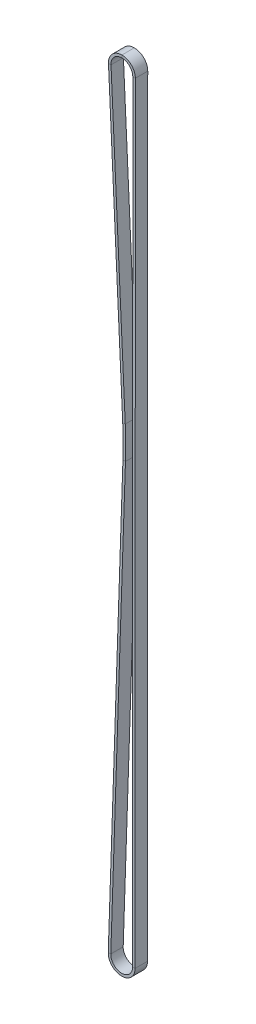
SolidWorks part; units mm, degrees
ref_plane "Front Plane" through (0, 0, 0) normal (0, 0, 1) x (1, 0, 0)
ref_plane "Top Plane" through (0, 0, 0) normal (0, 1, 0) x (1, 0, 0)
ref_plane "Right Plane" through (0, 0, 0) normal (1, 0, 0) x (0, 0, -1)
sketch "Sketch2" plane through (0, 0, 0) normal (0, 0, 1) x (1, 0, 0)
  line L0 (0, 0) -> (1, 0) construction
  line L1 (0, 0) -> (0, 1) construction
  line L3 (7.0911, -457.202) -> (7.2181, -0.002)
  line L4 (-7.2101, -0.338) -> (1.2395, -180.6057)
  line L5 (1.3637, -199.6863) -> (-7.3409, -456.9559)
  arc A0 (7.2181, -0.002) -> (-7.2101, -0.338) centre (0, 0) ccw
  arc A1 (-7.3409, -456.9559) -> (7.0911, -457.202) centre (-0.127, -457.2) ccw
  arc A2 (1.2395, -180.6057) -> (1.3637, -199.6863) centre (-235.126, -191.6848) cw
sketch "Sketch4" plane through (0, 0, 0) normal (1, 0, 0) x (0, 0, -1)
  line L0 (0, 7.2181) -> (0, -0.338) construction
  line L1 (-7.366, 7.9681) -> (0, 7.9681)
  line L2 (-7.366, 7.9681) -> (-7.366, 6.4681)
  line L3 (-7.366, 6.4681) -> (0, 6.4681)
  line L4 (0, 7.9681) -> (0, 6.4681)
  dimension "D1" = 7.366
  dimension "D2" = 1.5
sweep "Sweep1" add profiles "Sketch4" path "Sketch2"
